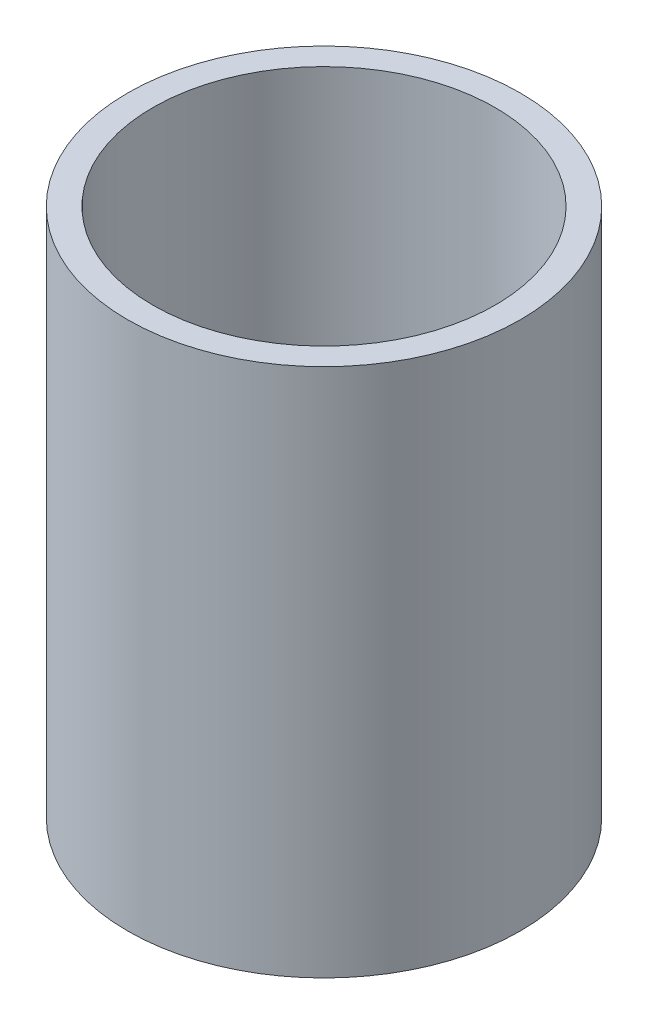
SolidWorks part; units mm, degrees
material "Corrugated Paper"
ref_plane "Front Plane" through (0, 0, 0) normal (0, 0, 1) x (1, 0, 0)
ref_plane "Top Plane" through (0, 0, 0) normal (0, 1, 0) x (1, 0, 0)
ref_plane "Right Plane" through (0, 0, 0) normal (1, 0, 0) x (0, 0, -1)
ref_axis "Axis1" through (0, 55, 0) along (0, -1, 0)
sketch "Sketch1" plane through (0, 0, 0) normal (0, 0, 1) x (1, 0, 0)
  line L1 (-49.4665, 45.6176) -> (-43.1165, 45.6176)
  line L2 (-49.4665, 45.6176) -> (-49.4665, -87.7324)
  line L3 (-49.4665, -87.7324) -> (-43.1165, -87.7324)
  line L4 (-43.1165, 45.6176) -> (-43.1165, -87.7324)
  line L5 (-38.1, 45.6176) -> (0, 45.6176) construction
  line L6 (-38.1, -87.7324) -> (0, -87.7324) construction
revolve "Revolve1" add sketch "Sketch1" angle 360 about axis through (0, 55, 0) along (0, -1, 0)
